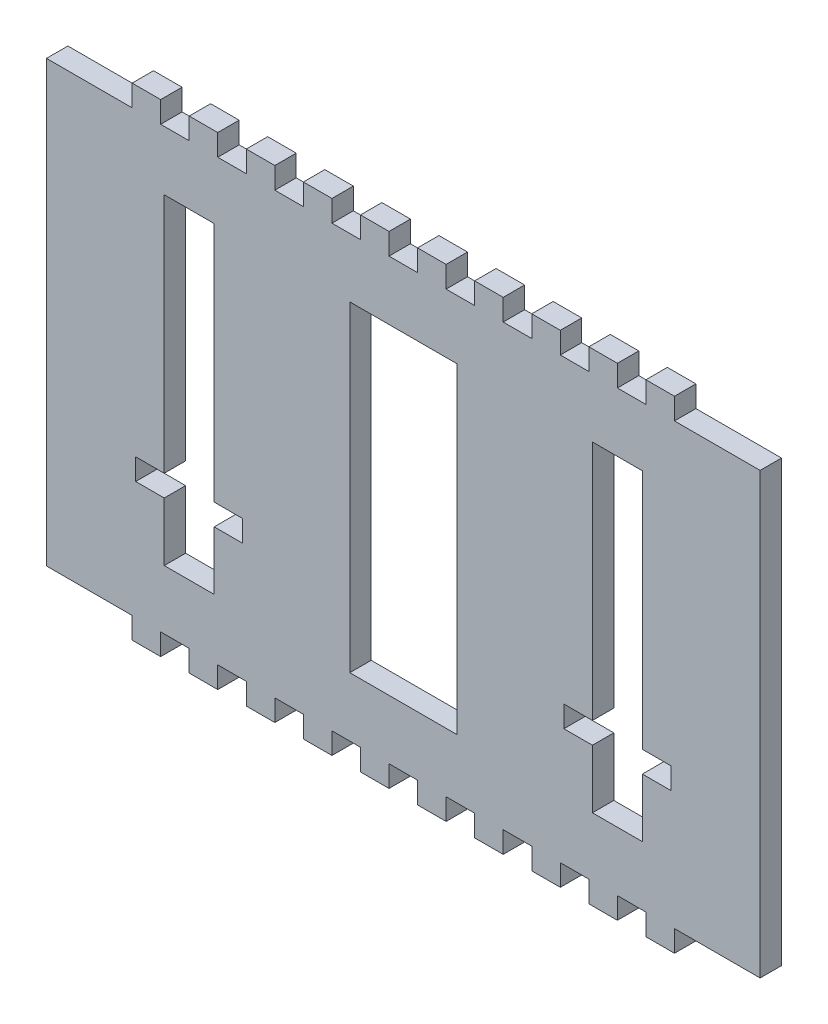
SolidWorks part; units mm, degrees
material "Acrylic (Medium-high impact)"
ref_plane "Ebene vorne" through (0, 0, 0) normal (0, 0, 1) x (1, 0, 0)
ref_plane "Ebene oben" through (0, 0, 0) normal (0, 1, 0) x (1, 0, 0)
ref_plane "Ebene rechts" through (0, 0, 0) normal (1, 0, 0) x (0, 0, -1)
sketch "Sketch1" plane through (0, 0, 0) normal (0, 0, 1) x (1, 0, 0)
  line L1 (50, -33.8) -> (-50, -33.8)
  line L2 (50, -33.8) -> (50, 33.8)
  line L3 (50, 33.8) -> (-50, 33.8)
  line L4 (-50, -33.8) -> (-50, 33.8)
  line L5 (50, -33.8) -> (-50, 33.8) construction
  line L6 (50, 33.8) -> (-50, -33.8) construction
  point P0 (0, 0)
  dimension "D1" = 100
  dimension "D2" = 67.6
extrude "Boss-Extrude1" add sketch "Sketch1" along normal blind 3
sketch "Sketch3" plane through (0, 0, 0) normal (0, 0, -1) x (-1, 0, 0)
  line L1 (-50, -33.8) -> (-46, -33.8)
  line L2 (-50, -33.8) -> (-50, -30.8)
  line L3 (-50, -30.8) -> (-46, -30.8)
  line L4 (-46, -33.8) -> (-46, -30.8)
  dimension "D1" = 4
  dimension "D2" = 3
extrude "Cut-Extrude1" cut sketch "Sketch3" against normal blind 10
pattern_linear "LPattern1" count 13 spacing 8 along (-1, 0, 0) of "Cut-Extrude1"
sketch "Sketch7" plane through (0, 0, 0) normal (0, 0, -1) x (-1, 0, 0)
  line L2 (7.5, -22.5) -> (-7.5, -22.5)
  line L3 (7.5, -22.5) -> (7.5, 22.5)
  line L4 (7.5, 22.5) -> (-7.5, 22.5)
  line L5 (-7.5, -22.5) -> (-7.5, 22.5)
  line L7 (7.5, -22.5) -> (-7.5, 22.5) construction
  line L8 (7.5, 22.5) -> (-7.5, -22.5) construction
  point P0 (0, 0)
  dimension "D1" = 15
  dimension "D2" = 45
extrude "Cut-Extrude5" cut sketch "Sketch7" against normal up to next (3 mm away)
mirror "Mirror1" about plane through (0, 0, 0) normal (0, 1, 0) of "LPattern1", "Cut-Extrude1"
pattern_linear "LPattern2" count 2 spacing 30 along (-1, 0, 0) count 2 spacing 30 along (1, 0, 0) of "Cut-Extrude5"
sketch "Sketch8" plane through (0, 0, 3) normal (0, 0, 1) x (1, 0, 0)
  line L2 (22.5, -14.3) -> (37.5, -14.3) construction
  line L3 (22.5, -22.5) -> (26.5, -22.5)
  line L4 (22.5, -22.5) -> (22.5, -14.3)
  line L6 (22.5, -14.3) -> (26.5, -14.3)
  line L8 (26.5, -22.5) -> (26.5, -14.3)
  line L9 (37.5, -22.5) -> (22.5, -22.5) construction
  line L10 (22.5, 22.5) -> (26.5, 22.5)
  line L11 (22.5, 22.5) -> (22.5, -11.3)
  line L12 (22.5, -11.3) -> (26.5, -11.3)
  line L13 (26.5, 22.5) -> (26.5, -11.3)
  line L14 (37.5, 22.5) -> (33.5, 22.5)
  line L15 (37.5, 22.5) -> (37.5, -11.3)
  line L16 (37.5, -11.3) -> (33.5, -11.3)
  line L17 (33.5, 22.5) -> (33.5, -11.3)
  line L18 (33.5, -22.5) -> (37.5, -22.5)
  line L19 (33.5, -22.5) -> (33.5, -14.3)
  line L20 (33.5, -14.3) -> (37.5, -14.3)
  line L21 (37.5, -22.5) -> (37.5, -14.3)
  line L22 (37.5, 22.5) -> (37.5, -22.5) construction
  line L23 (22.5, -11.3) -> (37.5, -11.3) construction
  dimension "D1" = 4
  dimension "D2" = 4
  dimension "D3" = 4
  dimension "D4" = 4
extrude "Boss-Extrude2" add sketch "Sketch8" against normal blind 3
mirror "Mirror2" about plane through (0, 0, 0) normal (1, 0, 0) of "Boss-Extrude2"
sketch "Sketch9" plane through (0, 0, 0) normal (0, 0, -1) x (-1, 0, 0)
  line L1 (-38, 33.8) -> (-50, 33.8)
  line L2 (-38, 33.8) -> (-38, 30.8)
  line L3 (-38, 30.8) -> (-50, 30.8)
  line L4 (-50, 33.8) -> (-50, 30.8)
  line L5 (38, 33.8) -> (50, 33.8)
  line L6 (38, 33.8) -> (38, 30.8)
  line L7 (38, 30.8) -> (50, 30.8)
  line L8 (50, 33.8) -> (50, 30.8)
  line L9 (50, -30.8) -> (38, -30.8)
  line L10 (50, -30.8) -> (50, -33.8)
  line L11 (50, -33.8) -> (38, -33.8)
  line L12 (38, -30.8) -> (38, -33.8)
  line L13 (-50, -30.8) -> (-38, -30.8)
  line L14 (-50, -30.8) -> (-50, -33.8)
  line L15 (-50, -33.8) -> (-38, -33.8)
  line L16 (-38, -30.8) -> (-38, -33.8)
extrude "Cut-Extrude6" cut sketch "Sketch9" against normal up to next
